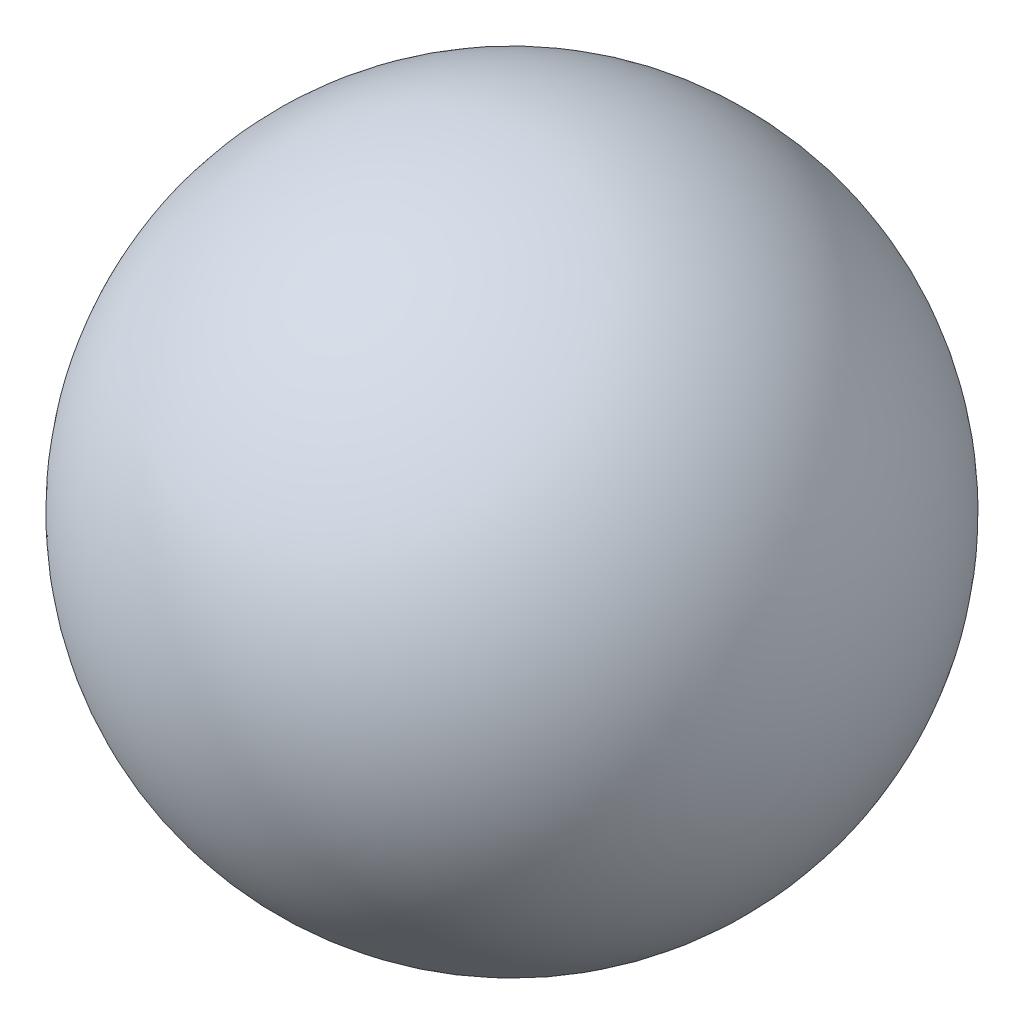
SolidWorks part; units mm, degrees
material "Cast Alloy Steel"
ref_plane "Front Plane" through (0, 0, 0) normal (0, 0, 1) x (1, 0, 0)
ref_plane "Top Plane" through (0, 0, 0) normal (0, 1, 0) x (1, 0, 0)
ref_plane "Right Plane" through (0, 0, 0) normal (1, 0, 0) x (0, 0, -1)
sketch "Sketch1" plane through (0, 0, 0) normal (0, 0, 1) x (1, 0, 0)
  line L0 (-12, 0) -> (12, 0)
  arc A2 (12, 0) -> (-12, 0) centre (0, 0) cw
  dimension "D1" = 12
revolve "Revolve1" add sketch "Sketch1" angle 360 about L0
